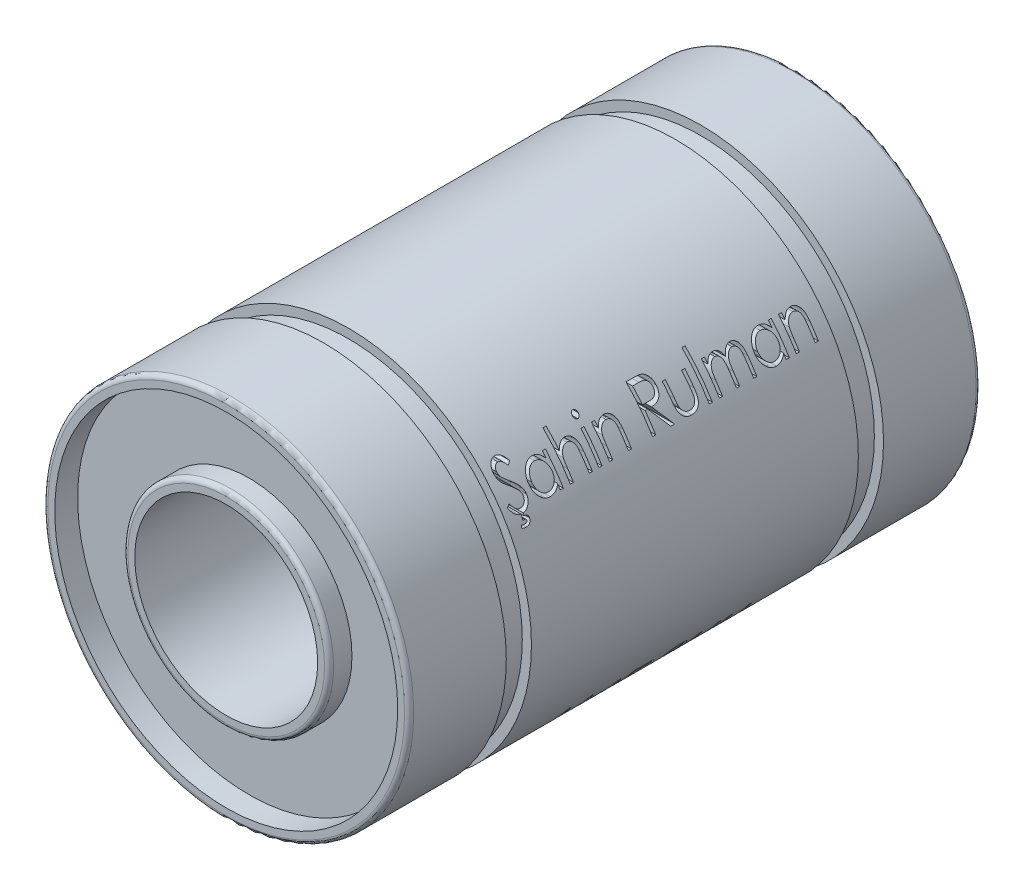
SolidWorks part; units mm, degrees
ref_plane "Front Plane" through (0, 0, 0) normal (0, 0, 1) x (1, 0, 0)
ref_plane "Top Plane" through (0, 0, 0) normal (0, 1, 0) x (1, 0, 0)
ref_plane "Right Plane" through (0, 0, 0) normal (1, 0, 0) x (0, 0, -1)
sketch "Sketch1" plane through (0, 0, 0) normal (0, 0, 1) x (1, 0, 0)
  circle A0 centre (0, 0) radius 4
  circle A1 centre (0, 0) radius 8
  dimension "D1" = 16
  dimension "D2" = 8
extrude "Boss-Extrude1" add sketch "Sketch1" along normal mid plane 25
sketch "Sketch2" plane through (0, 0, 0) normal (1, 0, 0) x (0, 0, -1)
  line L0 (-15.6816, 0) -> (13.7452, 0) construction
  line L2 (-8.25, 7.6) -> (-7.15, 7.6)
  line L3 (-8.25, 8.936) -> (-8.25, 7.6)
  line L4 (-7.15, 8.936) -> (-7.15, 7.6)
  line L5 (-8.25, 8.936) -> (-7.15, 8.936)
  line L6 (-15.6816, 7.6) -> (13.7452, 7.6) construction
  line L8 (-8.25, 8.936) -> (-8.25, -9.1264) construction
  line L10 (-7.15, 8.936) -> (-7.15, -9.1264) construction
  line L11 (8.25, 8.936) -> (7.15, 8.936)
  line L12 (7.15, 8.936) -> (7.15, 7.6)
  line L13 (8.25, 8.936) -> (8.25, 7.6)
  line L14 (8.25, 7.6) -> (7.15, 7.6)
  dimension "D1" = 7.6
  dimension "D3" = 1.1
revolve "Cut-Revolve1" cut sketch "Sketch2" angle 360 about L0
ref_plane "Plane1" through (9, 0, 0) normal (1, 0, 0) x (0, 0, -1)
sketch "Sketch3" plane through (9, 0, 0) normal (1, 0, 0) x (0, 0, -1)
  text T0 "Şahin Rulman\r\n\r\n\r\n     LME 8UU" font "Century Gothic" height 1.5
extrude "Cut-Extrude1" cut sketch "Sketch3" against normal blind 5
sketch "Sketch4" plane through (0, 0, 12.5) normal (0, 0, 1) x (1, 0, 0)
  circle A0 centre (0, 0) radius 4.5
  circle A1 centre (0, 0) radius 7.5
extrude "Cut-Extrude2" cut sketch "Sketch4" against normal blind 1
fillet "Fillet1" radius 0.2 2 edges at (4.5, 0, 12.5) (8, 0, 12.5)
mirror "Mirror2" about plane through (0, 0, 0) normal (0, 0, 1) of "Cut-Extrude2"
fillet "Fillet2" radius 0.2 2 edges at (4.5, 0, -12.5) (8, 0, -12.5)
